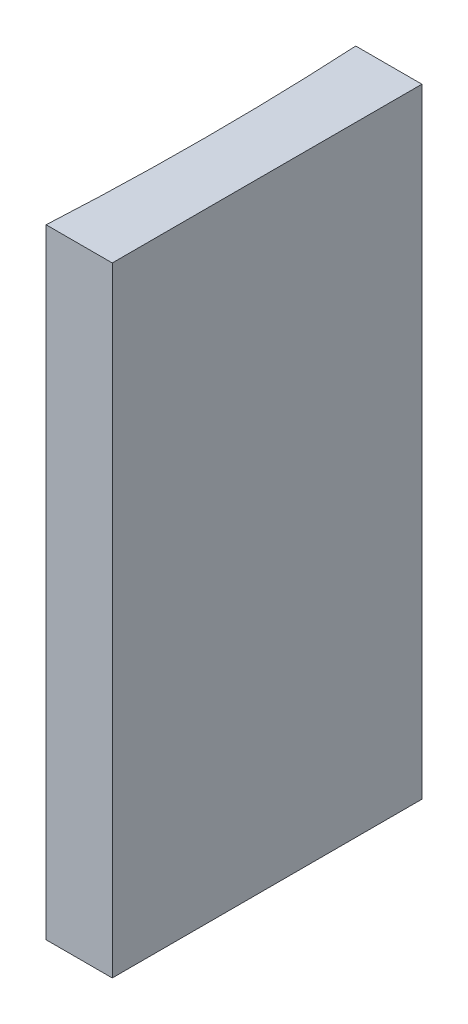
SolidWorks part; units mm, degrees
ref_plane "前视基准面" through (0, 0, 0) normal (0, 0, 1) x (1, 0, 0)
ref_plane "上视基准面" through (0, 0, 0) normal (0, 1, 0) x (1, 0, 0)
ref_plane "右视基准面" through (0, 0, 0) normal (1, 0, 0) x (0, 0, -1)
sketch "草图1" plane through (0, 0, 0) normal (0, 1, 0) x (1, 0, 0)
  line L0 (0, 0) -> (0, -10)
  line L1 (0, 0) -> (-2.1364, 0)
  line L2 (0, -10) -> (-2.1364, -10)
  line L3 (21.2259, -5) -> (-21.2259, -5) construction
  arc A0 (-2.1364, -10) -> (-2.1364, 0) centre (-93.7, -5) ccw
  point P7 (-2, -5)
  point P8 (0, -5)
  dimension "D2" = 91.7
  dimension "D3" = 2
  dimension "D1" = 10
extrude "凸台-拉伸1" add sketch "草图1" along normal blind 20
